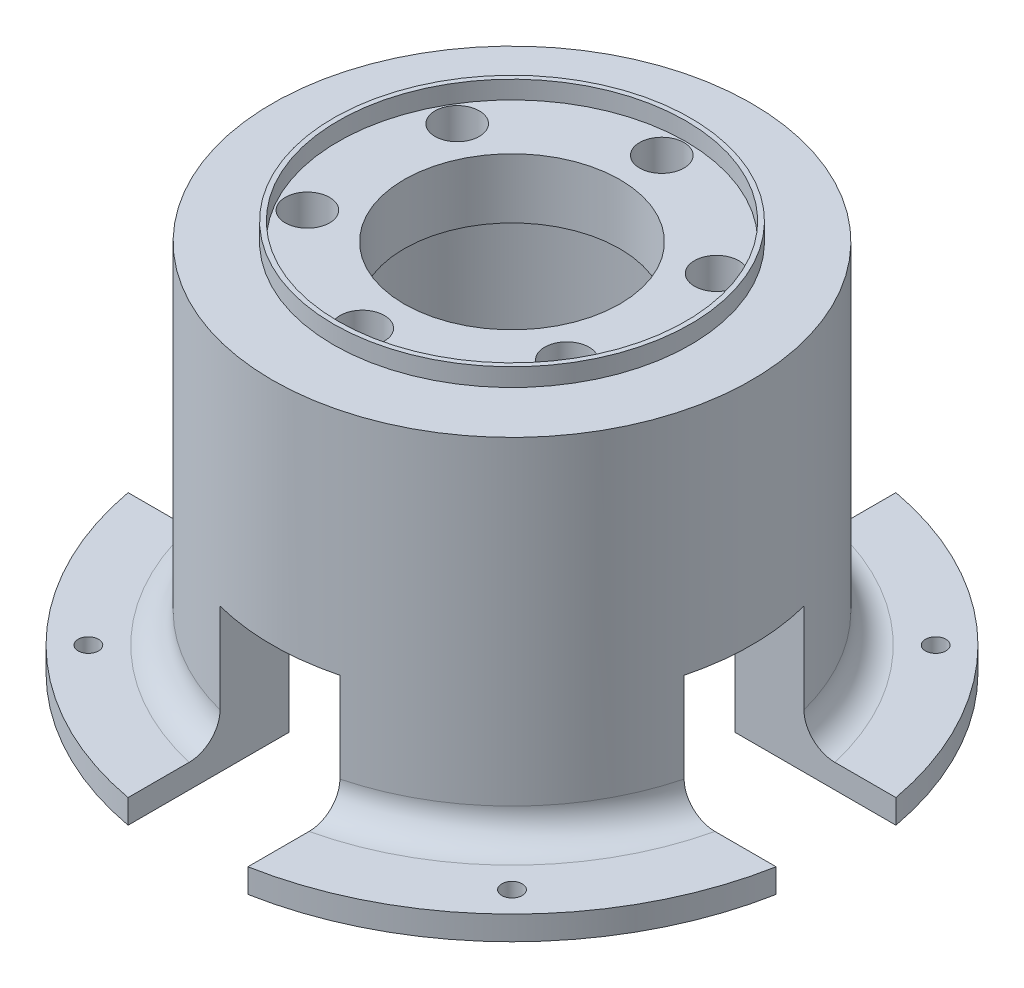
SolidWorks part; units mm, degrees
ref_plane "前视基准面" through (0, 0, 0) normal (0, 0, 1) x (1, 0, 0)
ref_plane "上视基准面" through (0, 0, 0) normal (0, 1, 0) x (1, 0, 0)
ref_plane "右视基准面" through (0, 0, 0) normal (1, 0, 0) x (0, 0, -1)
sketch "草图1" plane through (0, 0, 0) normal (0, 1, 0) x (1, 0, 0)
  circle A0 centre (0, 0) radius 55
  circle A1 centre (0, 0) radius 50 construction
  circle A2 centre (0, 50) radius 3.2 construction
  circle A3 centre (50, 0) radius 3.2 construction
  circle A4 centre (0, -50) radius 3.2 construction
  circle A5 centre (-50, 0) radius 3.2 construction
  point P14 (0, 0)
  dimension "D1" = 110
  dimension "D2" = 100
  dimension "D4" = 6.4
  dimension "D3" = 4
extrude "凸台-拉伸1" add sketch "草图1" along normal blind 10
sketch "草图2" plane through (0, 10, 0) normal (0, 1, 0) x (1, 0, 0)
  circle A0 centre (0, 0) radius 40
  circle A1 centre (0, 0) radius 29
  dimension "D1" = 80
  dimension "D2" = 58
extrude "凸台-拉伸2" add sketch "草图2" along normal blind 58.3
sketch "草图3" plane through (0, 68.3, 0) normal (0, 1, 0) x (1, 0, 0)
  circle A0 centre (0, 0) radius 29.8
  circle A1 centre (0, 0) radius 29
  dimension "D1" = 59.6
extrude "凸台-拉伸3" add sketch "草图3" along normal blind 3
sketch "草图6" plane through (0, 0, 0) normal (1, 0, 0) x (0, 0, -1)
  line L0 (0, -14.6399) -> (0, 79.9382) construction
  line L1 (40, 10) -> (-40, 10) construction
  line L2 (10, 10) -> (-10, 10)
  line L3 (10, 10) -> (10, 30)
  line L4 (10, 30) -> (-10, 30)
  line L5 (-10, 10) -> (-10, 30)
  dimension "D1" = 20
  dimension "D2" = 20
  dimension "D3" = 10
extrude "切除-拉伸3" cut sketch "草图6" against normal mid plane 111
pattern_circular "阵列(圆周)1" count 4 over 360 about axis through (0, 68.3, 0) along (0, -1, 0) of "切除-拉伸3"
sketch "草图9" plane through (0, 0, 0) normal (0, -1, 0) x (1, 0, 0)
  circle A0 centre (0, 0) radius 50 construction
  circle A1 centre (50, 0) radius 1.7
  circle A2 centre (35.3553, -35.3553) radius 1.7
  circle A3 centre (0, -50) radius 1.7
  circle A4 centre (-35.3553, -35.3553) radius 1.7
  circle A5 centre (-50, 0) radius 1.7
  circle A6 centre (-35.3553, 35.3553) radius 1.7
  circle A7 centre (0, 50) radius 1.7
  circle A8 centre (35.3553, 35.3553) radius 1.7
  point P23 (0, 0)
  dimension "D3" = 8
  dimension "D1" = 100
  dimension "D2" = 3.4
extrude "切除-拉伸6" cut sketch "草图9" against normal blind 10
sketch "草图10" plane through (0, 68.3, 0) normal (0, 1, 0) x (1, 0, 0)
  circle A0 centre (0, 0) radius 18
  circle A1 centre (0, 0) radius 29
  dimension "D1" = 36
extrude "凸台-拉伸4" add sketch "草图10" against normal blind 10
sketch "草图11" plane through (0, 68.3, 0) normal (0, 1, 0) x (1, 0, 0)
  circle A0 centre (0, 0) radius 25 construction
  circle A1 centre (0, -25) radius 1.7
  circle A2 centre (-21.6506, -12.5) radius 1.7
  circle A3 centre (-21.6506, 12.5) radius 1.7
  circle A4 centre (0, 25) radius 1.7
  circle A5 centre (21.6506, 12.5) radius 1.7
  circle A6 centre (21.6506, -12.5) radius 1.7
  point P17 (0, 0)
  dimension "D1" = 3.4
  dimension "D3" = 50
  dimension "D2" = 6
extrude "切除-拉伸7" cut sketch "草图11" against normal blind 10
sketch "草图12" plane through (0, 10, 0) normal (0, 1, 0) x (1, 0, 0)
  circle A0 centre (0, 0) radius 29
extrude "切除-拉伸8" cut sketch "草图12" against normal blind 10
sketch "草图13" plane through (0, 0, 0) normal (0, -1, 0) x (1, 0, 0)
  line L1 (-78.4183, 59.4672) -> (82.0125, 59.4672)
  line L2 (-78.4183, 59.4672) -> (-78.4183, -62.7347)
  line L3 (-78.4183, -62.7347) -> (82.0125, -62.7347)
  line L4 (82.0125, 59.4672) -> (82.0125, -62.7347)
extrude "切除-拉伸9" cut sketch "草图13" against normal offset from surface (6 mm away) 52.3 up to face at (-21.6506, 58.3, 14.2)
sketch "草图14" plane through (0, 68.3, 0) normal (0, 1, 0) x (1, 0, 0)
  circle A0 centre (21.6506, 12.5) radius 3.7
  circle A1 centre (21.6506, -12.5) radius 3.7
  circle A2 centre (0, -25) radius 3.7
  circle A3 centre (-21.6506, -12.5) radius 3.7
  circle A4 centre (-21.6506, 12.5) radius 3.7
  circle A5 centre (0, 25) radius 3.7
  point P15 (0, 0)
  dimension "D1" = 7.4
  dimension "D2" = 6
extrude "切除-拉伸10" cut sketch "草图14" against normal blind 5.5
sketch "草图15" plane through (0, 10, 0) normal (0, 1, 0) x (1, 0, 0)
  line L0 (10, 10) -> (59.5801, 10)
  line L1 (-60.1207, 10) -> (-10, 10)
  line L2 (-60.1207, 10) -> (-60.1207, -10)
  line L3 (-60.1207, -10) -> (-10, -10)
  line L4 (59.5801, 10) -> (59.5801, -10)
  line L5 (-10, 63.1303) -> (10, 63.1303)
  line L6 (-10, 63.1303) -> (-10, 10)
  line L7 (-10, -56.7482) -> (10, -56.7482)
  line L8 (10, 63.1303) -> (10, 10)
  line L9 (-10, -10) -> (-10, -56.7482)
  line L10 (10, -10) -> (59.5801, -10)
  line L11 (10, -10) -> (10, -56.7482)
extrude "切除-拉伸11" cut sketch "草图15" against normal blind 5.5
fillet "圆角1" radius 5 4 edges at (28.2843, 10, -28.2843) (-28.2843, 10, -28.2843) (28.2843, 10, 28.2843) (-28.2843, 10, 28.2843)
sketch "草图16" plane through (0, 6, 0) normal (0, -1, 0) x (1, 0, 0)
  circle A0 centre (0, 0) radius 50 construction
  circle A1 centre (0, -50) radius 1.7
  circle A2 centre (-43.3013, -25) radius 1.7
  circle A3 centre (-43.3013, 25) radius 1.7
  circle A4 centre (0, 50) radius 1.7
  circle A5 centre (43.3013, 25) radius 1.7
  circle A6 centre (43.3013, -25) radius 1.7
  point P17 (0, 0)
  dimension "D1" = 100
  dimension "D2" = 3.4
  dimension "D3" = 6
extrude "切除-拉伸12" [suppressed] cut sketch "草图16" against normal blind 10
